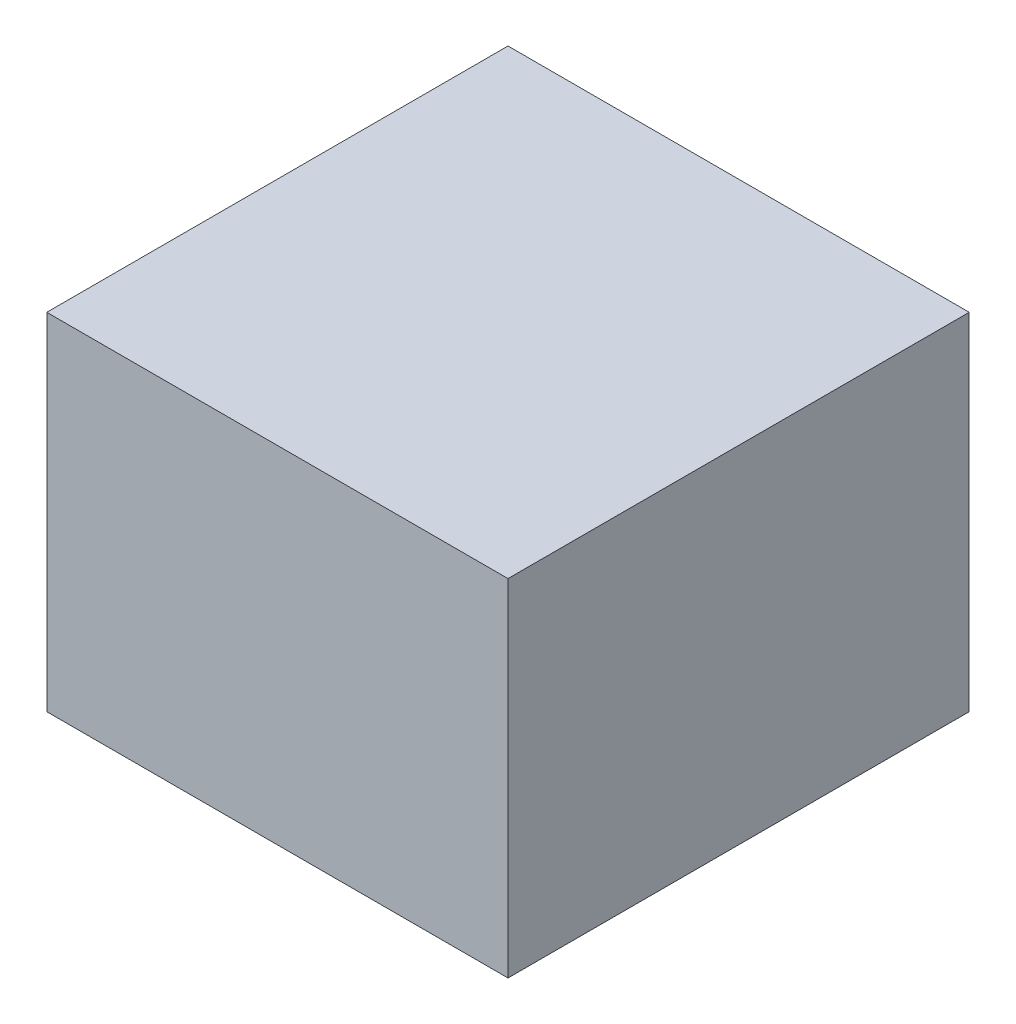
SolidWorks part; units mm, degrees
ref_plane "Front Plane" through (0, 0, 0) normal (0, 0, 1) x (1, 0, 0)
ref_plane "Top Plane" through (0, 0, 0) normal (0, 1, 0) x (1, 0, 0)
ref_plane "Right Plane" through (0, 0, 0) normal (1, 0, 0) x (0, 0, -1)
sketch "Sketch1" plane through (0, 0, 0) normal (0, 1, 0) x (1, 0, 0)
  line L1 (12.7, -12.7) -> (-12.7, -12.7)
  line L2 (12.7, -12.7) -> (12.7, 12.7)
  line L3 (12.7, 12.7) -> (-12.7, 12.7)
  line L4 (-12.7, -12.7) -> (-12.7, 12.7)
  line L5 (12.7, -12.7) -> (-12.7, 12.7) construction
  line L6 (12.7, 12.7) -> (-12.7, -12.7) construction
  point P0 (0, 0)
  dimension "D1" = 25.4
extrude "Boss-Extrude1" add sketch "Sketch1" along normal blind 19.05
equation "\".hf\"=0.1"
